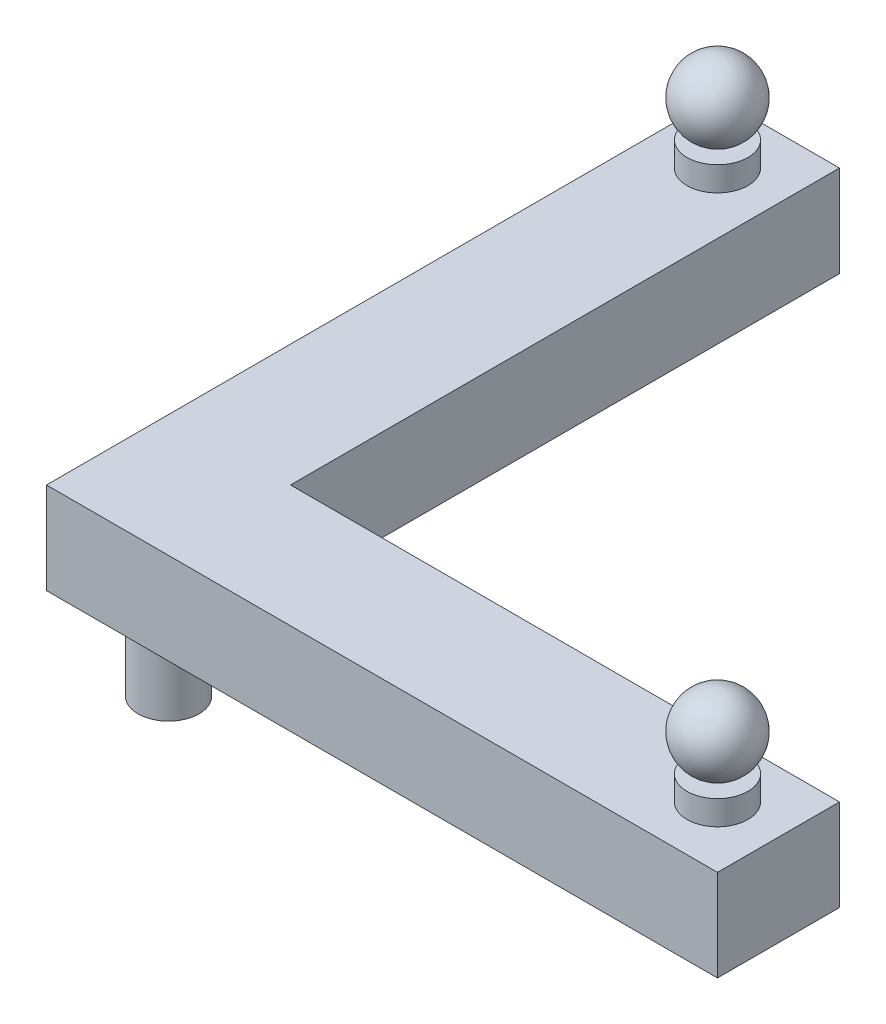
SolidWorks part; units mm, degrees
ref_plane "Front Plane" through (0, 0, 0) normal (0, 0, 1) x (1, 0, 0)
ref_plane "Top Plane" through (0, 0, 0) normal (0, 1, 0) x (1, 0, 0)
ref_plane "Right Plane" through (0, 0, 0) normal (1, 0, 0) x (0, 0, -1)
sketch "Sketch2" plane through (0, 0, 0) normal (0, 1, 0) x (1, 0, 0)
  line L0 (0, 139.7) -> (0, 0)
  line L1 (0, 0) -> (139.7, 0)
  line L2 (139.7, 0) -> (139.7, 25.4)
  line L3 (139.7, 25.4) -> (25.4, 25.4)
  line L4 (25.4, 25.4) -> (25.4, 139.7)
  line L5 (25.4, 139.7) -> (0, 139.7)
  dimension "D1" = 139.7
  dimension "D2" = 139.7
  dimension "D3" = 25.4
  dimension "D4" = 25.4
extrude "Boss-Extrude1" add sketch "Sketch2" along normal blind 19.05
sketch "Sketch3" plane through (0, 19.05, 0) normal (0, 1, 0) x (1, 0, 0)
  line L0 (139.7, 25.4) -> (25.4, 25.4) construction
  line L1 (139.7, 0) -> (139.7, 25.4) construction
  line L2 (25.4, 139.7) -> (0, 139.7) construction
  line L3 (25.4, 25.4) -> (25.4, 139.7) construction
  circle A0 centre (127, 12.7) radius 6.35
  circle A1 centre (12.7, 127) radius 6.35
  dimension "D1" = 12.7
  dimension "D4" = 12.7
  dimension "D2" = 12.7
  dimension "D3" = 12.7
  dimension "D5" = 12.7
  dimension "D6" = 12.7
extrude "Boss-Extrude2" add sketch "Sketch3" along normal blind 5.08
sketch "Sketch4" plane through (0, 0, 0) normal (0, -1, 0) x (1, 0, 0)
  line L1 (25.4, -25.4) -> (25.4, -139.7) construction
  line L2 (0, 0) -> (139.7, 0) construction
  circle A0 centre (12.7, -12.7) radius 6.35
  dimension "D1" = 12.7
  dimension "D2" = 12.7
  dimension "D3" = 12.7
extrude "Boss-Extrude3" add sketch "Sketch4" along normal blind 19.05
ref_plane "Plane1" through (0, 31.75, 0) normal (0, 1, 0) x (1, 0, 0)
sketch "Sketch5" plane through (0, 31.75, 0) normal (0, 1, 0) x (1, 0, 0)
  line L0 (5.08, 127) -> (20.32, 127)
  arc A0 (5.08, 127) -> (20.32, 127) centre (12.7, 127) ccw
  circle A1 centre (12.7, 127) radius 6.35 construction
  dimension "D1" = 15.24
  dimension "D2" = 0
revolve "Revolve1" add sketch "Sketch5" angle 360 about L0
sketch "Sketch6" plane through (0, 31.75, 0) normal (0, 1, 0) x (1, 0, 0)
  line L0 (119.38, 12.7) -> (134.62, 12.7)
  arc A0 (119.38, 12.7) -> (134.62, 12.7) centre (127, 12.7) ccw
  dimension "D1" = 15.24
revolve "Revolve2" add sketch "Sketch6" angle 360 about L0
